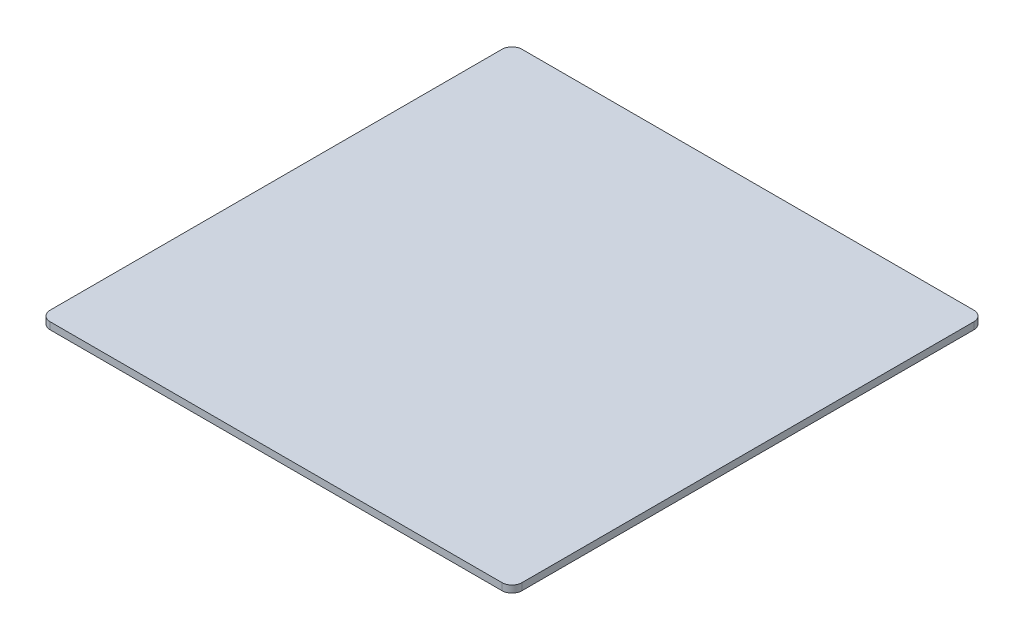
SolidWorks part; units mm, degrees
ref_plane "Front Plane" through (0, 0, 0) normal (0, 0, 1) x (1, 0, 0)
ref_plane "Top Plane" through (0, 0, 0) normal (0, 1, 0) x (1, 0, 0)
ref_plane "Right Plane" through (0, 0, 0) normal (1, 0, 0) x (0, 0, -1)
sketch "Sketch1" plane through (0, 0, 0) normal (0, 1, 0) x (1, 0, 0)
  line L1 (117.5, 117.5) -> (-117.5, 117.5)
  line L2 (117.5, 117.5) -> (117.5, -117.5)
  line L3 (117.5, -117.5) -> (-117.5, -117.5)
  line L4 (-117.5, 117.5) -> (-117.5, -117.5)
  line L5 (117.5, 117.5) -> (-117.5, -117.5) construction
  line L6 (117.5, -117.5) -> (-117.5, 117.5) construction
  point P0 (0, 0)
  dimension "D1" = 235
  dimension "D2" = 235
extrude "Boss-Extrude1" add sketch "Sketch1" along normal blind 3.5
fillet "Fillet1" radius 5 4 edges at (-117.5, 1.75, -117.5) (117.5, 1.75, -117.5) (117.5, 1.75, 117.5) (-117.5, 1.75, 117.5)
sketch "Sketch2" plane through (0, 0, 0) normal (0, -1, 0) x (1, 0, 0)
  line L0 (0, 0) -> (-116.0355, -116.0355) construction
  line L1 (0, 0) -> (-117.5, 0) construction
  line L2 (-117.5, -112.5) -> (-117.5, 112.5) construction
  arc A0 (-117.5, -112.5) -> (-112.5, -117.5) centre (-112.5, -112.5) ccw construction
  circle A1 centre (-85, -85) radius 2
  dimension "D2" = 4
  dimension "D1" = 85
extrude "Cut-Extrude1" cut sketch "Sketch2" against normal blind 1
pattern_linear "LPattern1" count 2 spacing 170 along (0, 0, 1) count 2 spacing 170 along (1, 0, 0) of "Cut-Extrude1"
